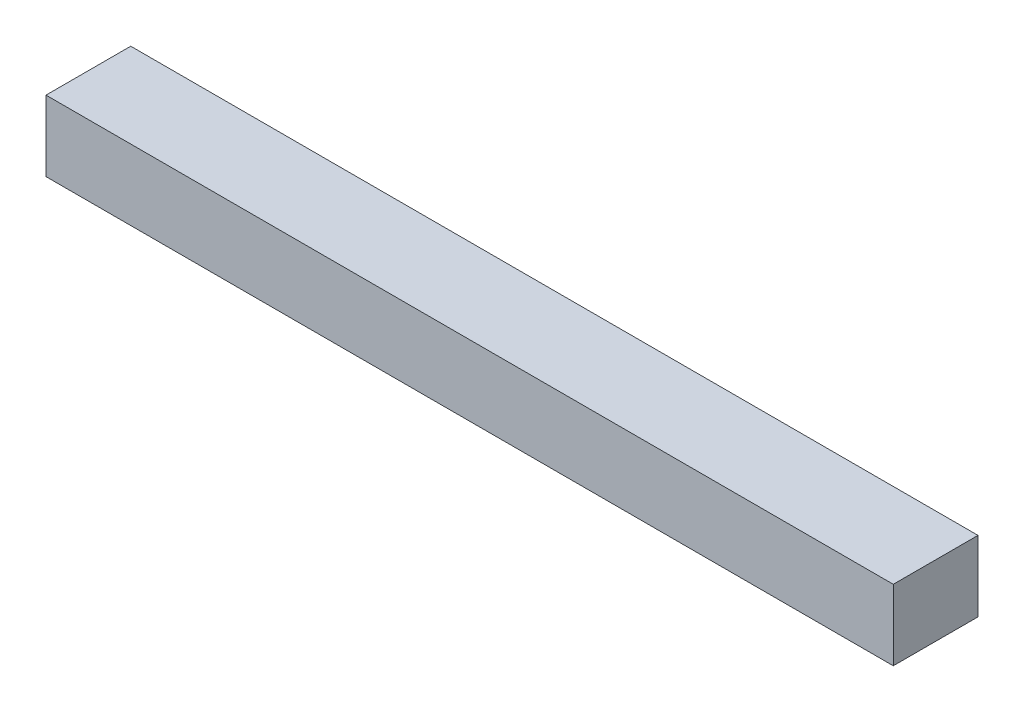
SolidWorks part; units mm, degrees
ref_plane "Спереди" through (0, 0, 0) normal (0, 0, 1) x (1, 0, 0)
ref_plane "Сверху" through (0, 0, 0) normal (0, 1, 0) x (1, 0, 0)
ref_plane "Справа" through (0, 0, 0) normal (1, 0, 0) x (0, 0, -1)
sketch "Эскиз2" plane through (0, 0, 0) normal (1, 0, 0) x (0, 0, -1)
  line L1 (-15, -12.5) -> (15, -12.5)
  line L2 (-15, -12.5) -> (-15, 12.5)
  line L3 (-15, 12.5) -> (15, 12.5)
  line L4 (15, -12.5) -> (15, 12.5)
  line L5 (-15, -12.5) -> (15, 12.5) construction
  line L6 (-15, 12.5) -> (15, -12.5) construction
  point P0 (0, 0)
extrude "Бобышка-Вытянуть1" add sketch "Эскиз2" along normal blind 300
